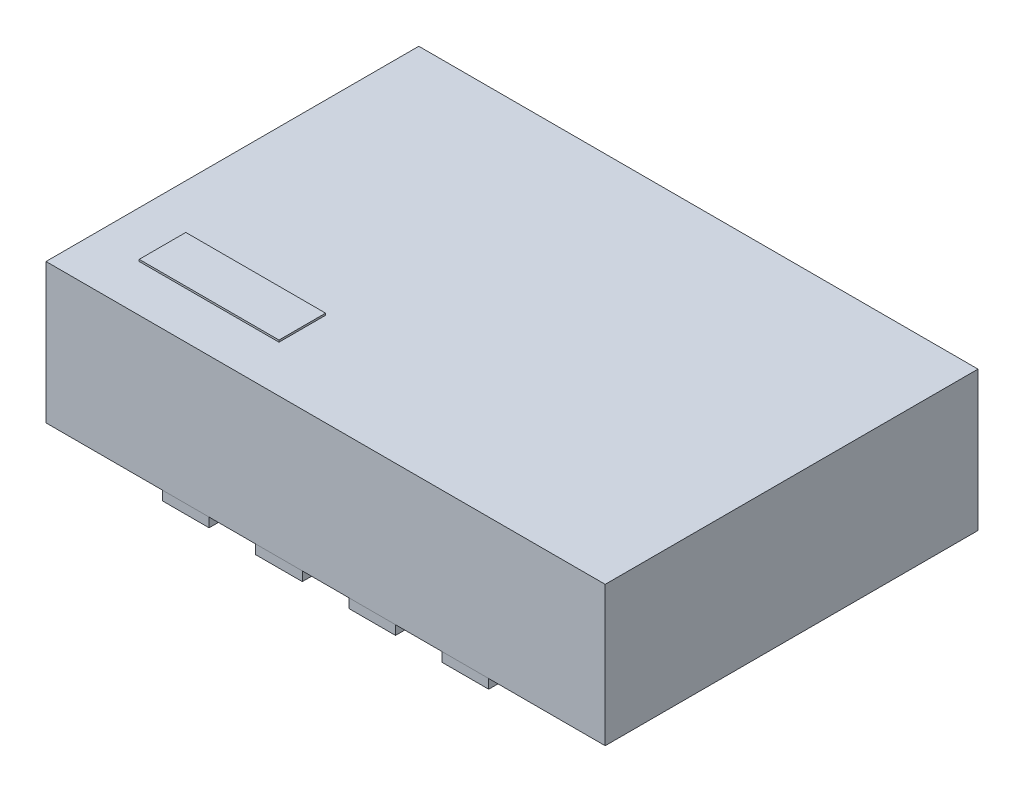
SolidWorks part; units mm, degrees
ref_plane "Ebene vorne" through (0, 0, 0) normal (0, 0, 1) x (1, 0, 0)
ref_plane "Ebene oben" through (0, 0, 0) normal (0, 1, 0) x (1, 0, 0)
ref_plane "Ebene rechts" through (0, 0, 0) normal (1, 0, 0) x (0, 0, -1)
sketch "Skizze1" plane through (0, 0, 0) normal (0, 1, 0) x (1, 0, 0)
  line L0 (-0.9086, -0.5164) -> (-1.0414, -0.3836)
  line L1 (-0.7672, -0.575) -> (0.9, -0.575)
  line L2 (-1.1, -0.2422) -> (-1.1, 0.375)
  line L3 (-0.9, 0.575) -> (0.9, 0.575)
  line L4 (1.1, -0.375) -> (1.1, 0.375)
  line L5 (-1.1, -0.575) -> (1.1, 0.575) construction
  line L6 (-1.1, 0.575) -> (1.1, -0.575) construction
  line L8 (-0.255, -0.65) -> (-0.245, -0.65)
  line L9 (-0.375, -0.77) -> (-0.375, -1)
  line L10 (-0.375, -1) -> (-0.125, -1)
  line L11 (-0.125, -0.77) -> (-0.125, -1)
  line L12 (-0.375, -0.65) -> (-0.125, -1) construction
  line L13 (-0.375, -1) -> (-0.125, -0.65) construction
  line L14 (0.125, -1) -> (0.375, -1)
  line L15 (0.125, -1) -> (0.125, -0.77)
  line L16 (0.245, -0.65) -> (0.255, -0.65)
  line L17 (0.375, -1) -> (0.375, -0.77)
  line L18 (0.125, -1) -> (0.375, -0.65) construction
  line L19 (0.125, -0.65) -> (0.375, -1) construction
  line L20 (0.625, -1) -> (0.875, -1)
  line L21 (0.625, -1) -> (0.625, -0.77)
  line L22 (0.745, -0.65) -> (0.755, -0.65)
  line L23 (0.875, -1) -> (0.875, -0.77)
  line L24 (0.625, -1) -> (0.875, -0.65) construction
  line L25 (0.625, -0.65) -> (0.875, -1) construction
  line L26 (-0.625, -1) -> (-0.875, -1)
  line L27 (-0.625, -1) -> (-0.625, -0.77)
  line L28 (-0.745, -0.65) -> (-0.755, -0.65)
  line L29 (-0.875, -1) -> (-0.875, -0.77)
  line L30 (-0.625, -1) -> (-0.875, -0.65) construction
  line L31 (-0.625, -0.65) -> (-0.875, -1) construction
  line L32 (-0.375, 1) -> (-0.125, 1)
  line L33 (-0.375, 1) -> (-0.375, 0.77)
  line L34 (-0.255, 0.65) -> (-0.245, 0.65)
  line L35 (-0.125, 1) -> (-0.125, 0.77)
  line L36 (-0.375, 1) -> (-0.125, 0.65) construction
  line L37 (-0.375, 0.65) -> (-0.125, 1) construction
  line L38 (-0.745, 0.65) -> (-0.755, 0.65)
  line L39 (-0.625, 0.77) -> (-0.625, 1)
  line L40 (-0.625, 1) -> (-0.875, 1)
  line L41 (-0.875, 0.77) -> (-0.875, 1)
  line L42 (-0.625, 0.65) -> (-0.875, 1) construction
  line L43 (-0.625, 1) -> (-0.875, 0.65) construction
  line L44 (0.245, 0.65) -> (0.255, 0.65)
  line L45 (0.125, 0.77) -> (0.125, 1)
  line L46 (0.125, 1) -> (0.375, 1)
  line L47 (0.375, 0.77) -> (0.375, 1)
  line L48 (0.125, 0.65) -> (0.375, 1) construction
  line L49 (0.125, 1) -> (0.375, 0.65) construction
  line L50 (0.745, 0.65) -> (0.755, 0.65)
  line L51 (0.625, 0.77) -> (0.625, 1)
  line L52 (0.625, 1) -> (0.875, 1)
  line L53 (0.875, 0.77) -> (0.875, 1)
  line L54 (0.625, 0.65) -> (0.875, 1) construction
  line L55 (0.625, 1) -> (0.875, 0.65) construction
  arc A0 (0.9, 0.575) -> (1.1, 0.375) centre (0.9, 0.375) cw
  arc A1 (-0.9, 0.575) -> (-1.1, 0.375) centre (-0.9, 0.375) ccw
  arc A2 (1.1, -0.375) -> (0.9, -0.575) centre (0.9, -0.375) cw
  arc A3 (-0.7672, -0.575) -> (-0.9086, -0.5164) centre (-0.7672, -0.375) cw
  arc A4 (-1.0414, -0.3836) -> (-1.1, -0.2422) centre (-0.9, -0.2422) cw
  arc A5 (-0.375, -0.77) -> (-0.255, -0.65) centre (-0.255, -0.77) cw
  arc A6 (-0.245, -0.65) -> (-0.125, -0.77) centre (-0.245, -0.77) cw
  arc A7 (-0.755, -0.65) -> (-0.875, -0.77) centre (-0.755, -0.77) ccw
  arc A8 (-0.625, -0.77) -> (-0.745, -0.65) centre (-0.745, -0.77) ccw
  arc A9 (0.245, -0.65) -> (0.125, -0.77) centre (0.245, -0.77) ccw
  arc A10 (0.375, -0.77) -> (0.255, -0.65) centre (0.255, -0.77) ccw
  arc A11 (0.745, -0.65) -> (0.625, -0.77) centre (0.745, -0.77) ccw
  arc A12 (0.875, -0.77) -> (0.755, -0.65) centre (0.755, -0.77) ccw
  arc A13 (-0.755, 0.65) -> (-0.875, 0.77) centre (-0.755, 0.77) cw
  arc A14 (-0.625, 0.77) -> (-0.745, 0.65) centre (-0.745, 0.77) cw
  arc A15 (-0.255, 0.65) -> (-0.375, 0.77) centre (-0.255, 0.77) cw
  arc A16 (-0.125, 0.77) -> (-0.245, 0.65) centre (-0.245, 0.77) cw
  arc A17 (0.245, 0.65) -> (0.125, 0.77) centre (0.245, 0.77) cw
  arc A18 (0.375, 0.77) -> (0.255, 0.65) centre (0.255, 0.77) cw
  arc A19 (0.745, 0.65) -> (0.625, 0.77) centre (0.745, 0.77) cw
  arc A20 (0.875, 0.77) -> (0.755, 0.65) centre (0.755, 0.77) cw
  point P0 (0, 0)
  point P19 (-0.85, -0.575)
  point P22 (-1.1, -0.325)
  point P23 (-0.25, -0.825)
  point P34 (0.25, -0.825)
  point P39 (0.75, -0.825)
  point P44 (-0.75, -0.825)
  point P67 (-0.25, 0.825)
  point P72 (-0.75, 0.825)
  point P77 (0.25, 0.825)
  point P82 (0.75, 0.825)
  dimension "D3" = 0.2
  dimension "D4" = 0.2
  dimension "D6" = 0.2
  dimension "D7" = 0.2
  dimension "D8" = 0.2
  dimension "D12" = 0.12
  dimension "D13" = 0.12
  dimension "D27" = 0.12
  dimension "D28" = 0.12
  dimension "D29" = 0.12
  dimension "D30" = 0.12
  dimension "D31" = 0.12
  dimension "D32" = 0.12
  dimension "D49" = 0.12
  dimension "D50" = 0.12
  dimension "D51" = 0.12
  dimension "D52" = 0.12
  dimension "D53" = 0.12
  dimension "D54" = 0.12
  dimension "D55" = 0.12
  dimension "D56" = 0.12
  dimension "D1" = 2.2
  dimension "D2" = 1.15
  dimension "D9" = 0.25
  dimension "D10" = 0.35
  dimension "D11" = 1
  dimension "D14" = 0.25
  dimension "D15" = 0.5
  dimension "D16" = 0.5
  dimension "D17" = 0.5
  dimension "D18" = 0.25
  dimension "D19" = 0.25
  dimension "D20" = 0.25
  dimension "D21" = 1
  dimension "D22" = 1
  dimension "D23" = 1
  dimension "D24" = 0.35
  dimension "D25" = 0.35
  dimension "D26" = 0.35
  dimension "D33" = 0.25
  dimension "D34" = 0.25
  dimension "D35" = 0.25
  dimension "D36" = 0.25
  dimension "D37" = 0.35
  dimension "D38" = 0.35
  dimension "D39" = 0.35
  dimension "D40" = 0.35
  dimension "D41" = 1
  dimension "D42" = 1
  dimension "D43" = 1
  dimension "D44" = 1
  dimension "D45" = 0.25
  dimension "D46" = 0.5
  dimension "D47" = 0.5
  dimension "D48" = 0.5
extrude "Aufsatz-Linear austragen1" add sketch "Skizze1" along normal blind 0.05
sketch "Skizze2" plane through (0, 0.05, 0) normal (0, 1, 0) x (1, 0, 0)
  line L1 (-1.5, 1) -> (1.5, 1)
  line L2 (-1.5, 1) -> (-1.5, -1)
  line L3 (-1.5, -1) -> (1.5, -1)
  line L4 (1.5, 1) -> (1.5, -1)
  line L5 (-1.5, 1) -> (1.5, -1) construction
  line L6 (-1.5, -1) -> (1.5, 1) construction
  point P0 (0, 0)
  dimension "D1" = 3
  dimension "D2" = 2
extrude "Aufsatz-Linear austragen3" add sketch "Skizze2" along normal blind 0.75 separate body
sketch "Skizze3" plane through (0, 0.8, 0) normal (0, 1, 0) x (1, 0, 0)
  line L0 (-1.5, 1) -> (-1.5, -1) construction
  line L1 (-1.25, -0.5) -> (-0.5, -0.5)
  line L2 (-1.25, -0.5) -> (-1.25, -0.75)
  line L3 (-1.25, -0.75) -> (-0.5, -0.75)
  line L4 (-0.5, -0.5) -> (-0.5, -0.75)
  line L5 (-1.25, -0.5) -> (-0.5, -0.75) construction
  line L6 (-1.25, -0.75) -> (-0.5, -0.5) construction
  line L7 (-1.5, -1) -> (1.5, -1) construction
  point P0 (-0.875, -0.625)
  dimension "D1" = 0.75
  dimension "D2" = 0.25
  dimension "D3" = 0.25
  dimension "D4" = 0.25
extrude "Aufsatz-Linear austragen4" add sketch "Skizze3" along normal blind 0.01
